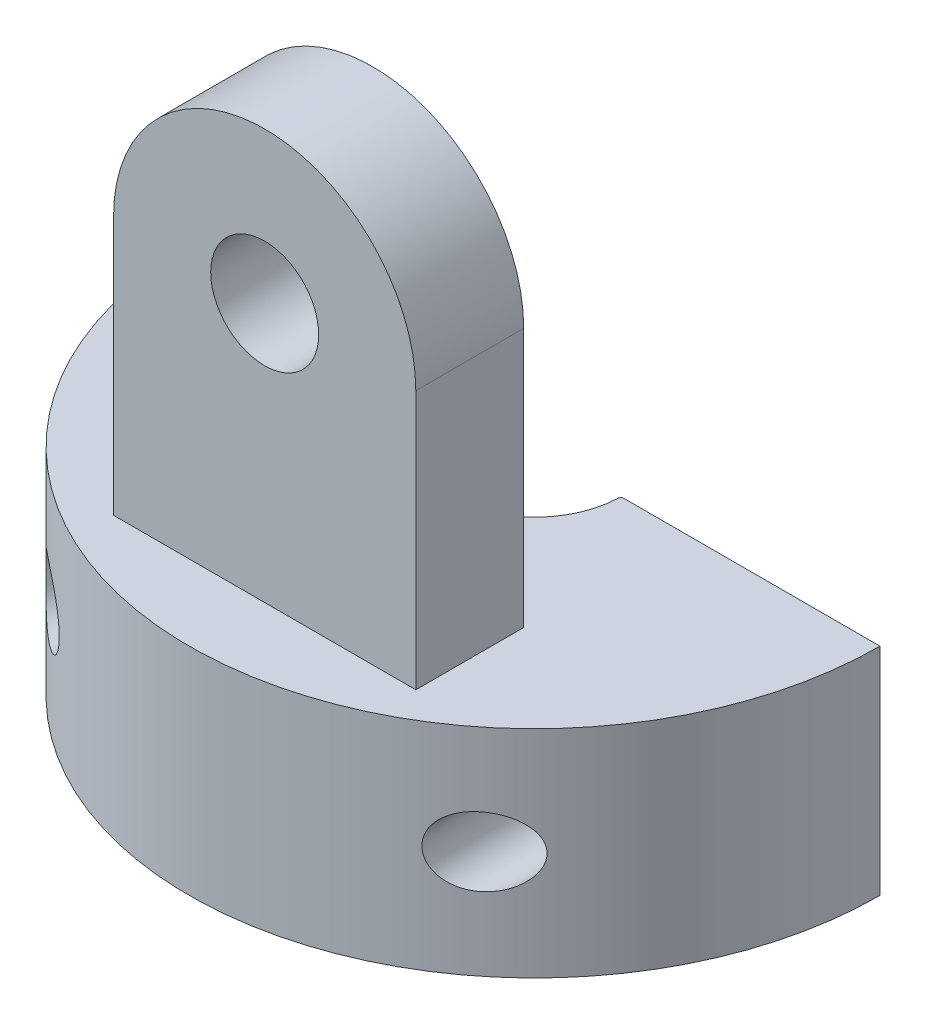
SolidWorks part; units mm, degrees
material "6061 Alloy"
ref_plane "Front Plane" through (0, 0, 0) normal (0, 0, 1) x (1, 0, 0)
ref_plane "Top Plane" through (0, 0, 0) normal (0, 1, 0) x (1, 0, 0)
ref_plane "Right Plane" through (0, 0, 0) normal (1, 0, 0) x (0, 0, -1)
sketch "Sketch1" plane through (0, 0, 0) normal (0, 1, 0) x (1, 0, 0)
  line L0 (2, 0) -> (8, 0)
  line L1 (-2, 0) -> (-8, 0)
  arc A0 (-8, 0) -> (8, 0) centre (0, 0) ccw
  arc A1 (2, 0) -> (-2, 0) centre (0, 0) cw
  dimension "D1" = 2
  dimension "D2" = 8
extrude "Boss-Extrude1" add sketch "Sketch1" along normal mid plane 5 contours L0 A0 L1 A1
sketch "Sketch2" plane through (0, 2.5, 0) normal (0, 1, 0) x (1, 0, 0)
  line L0 (3.5, -3.75) -> (-3.5, -3.75)
  line L1 (-3.5, -3.75) -> (-3.5, -6.25)
  line L2 (3.5, -6.25) -> (3.5, -3.75)
  line L3 (3.5, -6.25) -> (-3.5, -6.25)
  arc A0 (-3.5, -6.25) -> (3.5, -6.25) centre (0, 0) ccw construction
  arc A1 (-8, 0) -> (8, 0) centre (0, 0) ccw construction
  dimension "D1" = 2.5
  dimension "D2" = 3.75
  dimension "D3" = 7
extrude "Boss-Extrude2" add sketch "Sketch2" along normal blind 9.5 contours L2 L0 L1 L3
sketch "Sketch3" plane through (0, 0, 3.75) normal (0, 0, -1) x (-1, 0, 0)
  line L0 (3.5, 12) -> (3.5, 2.5) construction
  line L1 (-3.5, 8.5) -> (-3.5, 14.8864)
  line L2 (-3.5, 14.8864) -> (0, 16.8092)
  line L3 (0, 16.8092) -> (3.5, 14.5)
  line L4 (3.5, 14.5) -> (3.5, 8.5)
  line L6 (-3.5, 12) -> (3.5, 12) construction
  line L7 (-3.5, 12) -> (-3.5, 2.5) construction
  arc A0 (3.5, 8.5) -> (-3.5, 8.5) centre (0, 8.5) ccw
extrude "Cut-Extrude1" cut sketch "Sketch3" against normal blind 9.5 contours L3 L4 A0 L1 L2
sketch "Sketch4" plane through (0, 0, 3.75) normal (0, 0, -1) x (-1, 0, 0)
  circle A0 centre (0, 8.5) radius 1.25
  dimension "D1" = 2.5
extrude "Cut-Extrude2" cut sketch "Sketch4" against normal blind 9.5
sketch "Sketch9" plane through (0, 0, 0) normal (0, 0, 1) x (1, 0, 0)
  line L0 (0, 0.5) -> (-3, 2.5)
  line L1 (-2, 2.5) -> (-8, 2.5) construction
  line L2 (-3, 2.5) -> (0, 2.5)
  line L3 (0, 2.5) -> (0, 0.5)
  dimension "D1" = 3
  dimension "D2" = 2
hole_wizard "M2x0.4 Tapped Hole1" positions "Sketch10" profile "Sketch11" tap size "M2x0.4" standard "ANSI Metric" end condition through all
sketch "Sketch10" plane through (0, 0, 0) normal (0, 0, -1) x (-1, 0, 0)
  point P0 (-5, 0)
  point P2 (5, 0)
  dimension "D1" = 5
  dimension "D2" = 5
sketch "Sketch11" plane through (5, 0, 0) normal (1, 0, 0) x (0, 1, 0)
  line L0 (0, 0) -> (0, 8)
  line L1 (0, 8) -> (0.8, 8)
  line L2 (0.8, 8) -> (0.8, 0)
  line L5 (0.8, 0) -> (0, 0)
  line L11 (0, -6.35) -> (0, 107.95) construction
  dimension "Thru Tap Drill Dia." = 1.6
  dimension "Thru Tap Drill Depth" = 8
cosmetic thread "Hole Thread1" parameters "D2"=2
cosmetic thread "Hole Thread2" parameters "D2"=2
fillet "Fillet1" radius 0.07 2 edges at (-2, 0, 0) (2, 0, 0)
